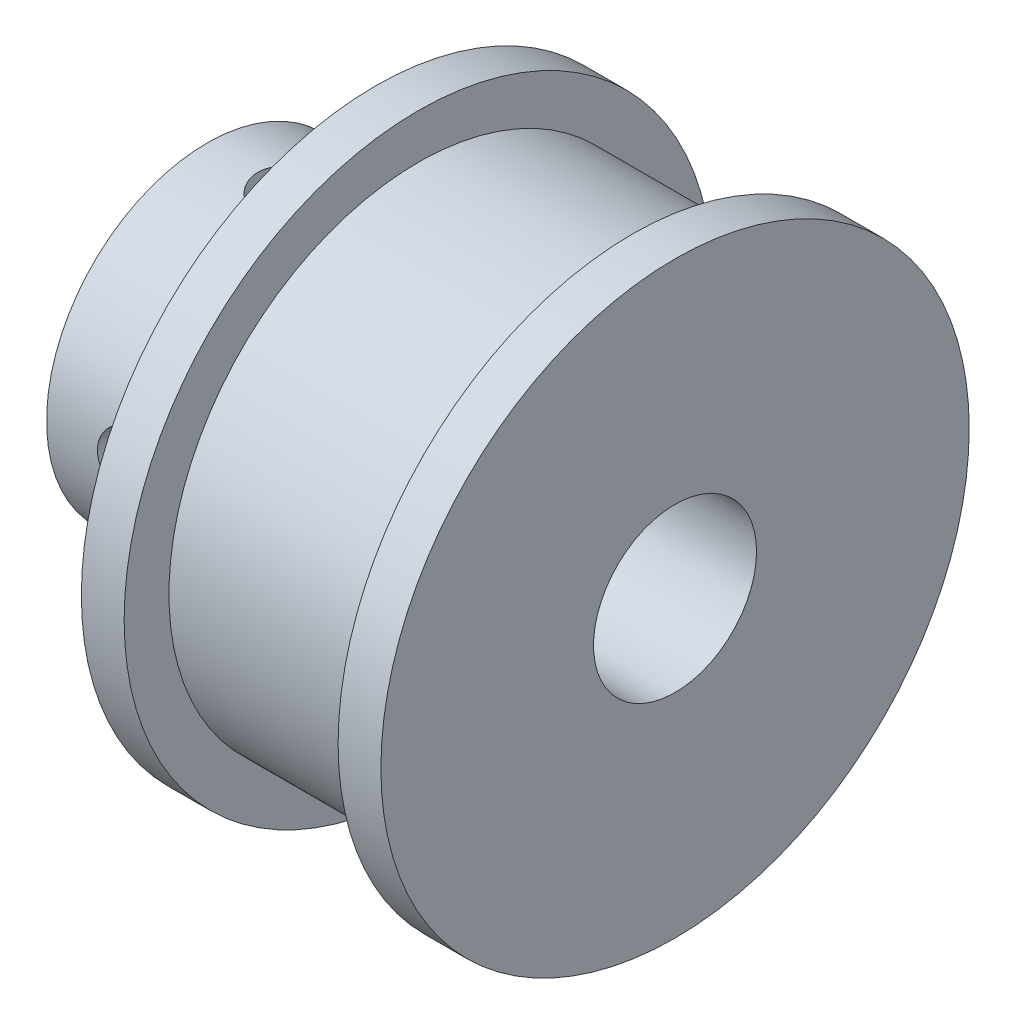
SolidWorks part; units mm, degrees
material "6061-T6 (SS)"
ref_plane "Front Plane" through (0, 0, 0) normal (0, 0, 1) x (1, 0, 0)
ref_plane "Top Plane" through (0, 0, 0) normal (0, 1, 0) x (1, 0, 0)
ref_plane "Right Plane" through (0, 0, 0) normal (1, 0, 0) x (0, 0, -1)
sketch "Sketch1" plane through (0, 0, 0) normal (0, 0, 1) x (1, 0, 0)
  line L0 (0, 2.5) -> (0, 6)
  line L1 (6.3, 11) -> (7.9, 11)
  line L2 (7.9, 11) -> (7.9, 9.325)
  line L3 (7.9, 9.325) -> (15.9, 9.325)
  line L4 (15.9, 9.325) -> (15.9, 11)
  line L5 (15.9, 11) -> (17.5, 11)
  line L6 (17.5, 11) -> (17.5, 2.5)
  line L7 (17.5, 2.5) -> (0, 2.5)
  line L8 (0, 0) -> (-7.6744, 0) construction
  line L9 (6.3, 11) -> (6.3, 6)
  line L10 (6.3, 6) -> (0, 6)
  dimension "D1" = 5
  dimension "D2" = 22
  dimension "D3" = 18.65
  dimension "D4" = 11.2
  dimension "D5" = 17.5
  dimension "D6" = 1.6
  dimension "D7" = 12
revolve "Revolve1" add sketch "Sketch1" angle 360 about L8
hole_wizard "M3x0.5 Tapped Hole1" positions "Sketch3" profile "Sketch2" tap size "M3x0.5" standard "ANSI Metric"
sketch "Sketch3" plane through (0, 0, 0) normal (0, 1, 0) x (1, 0, 0)
  line L0 (0, 0) -> (6.3, 0) construction
  line L2 (6.3, 6) -> (6.3, -6) construction
  point P8 (3.15, 0)
sketch "Sketch2" plane through (3.15, 0, 0) normal (1, 0, 0) x (0, 0, -1)
  line L0 (0, 0) -> (0, 11)
  line L1 (0, 11) -> (1.25, 11)
  line L2 (1.25, 11) -> (1.25, 0)
  line L5 (1.25, 0) -> (0, 0)
  line L11 (0, -6.35) -> (0, 107.95) construction
  dimension "Thread Major Dia." = 2.5
  dimension "Thru Tap Drill Depth" = 11
hole_wizard "M3x0.5 Tapped Hole2" positions "Sketch5" profile "Sketch4" tap size "M3x0.5" standard "ANSI Metric"
sketch "Sketch5" plane through (0, 0, 0) normal (0, 0, 1) x (1, 0, 0)
  line L0 (0, 0) -> (6.3, 0) construction
  line L2 (6.3, 11) -> (6.3, -11) construction
  point P7 (3.15, 0)
sketch "Sketch4" plane through (3.15, 0, 0) normal (1, 0, 0) x (0, 1, 0)
  line L0 (0, 0) -> (0, 11)
  line L1 (0, 11) -> (1.25, 11)
  line L2 (1.25, 11) -> (1.25, 0)
  line L5 (1.25, 0) -> (0, 0)
  line L11 (0, -6.35) -> (0, 107.95) construction
  dimension "Thread Major Dia." = 2.5
  dimension "Thru Tap Drill Depth" = 11
sketch "Sketch6" plane through (17.5, 0, 0) normal (1, 0, 0) x (0, 0, -1)
  circle A0 centre (0, 0) radius 3.048
extrude "Cut-Extrude1" cut sketch "Sketch6" against normal through all
